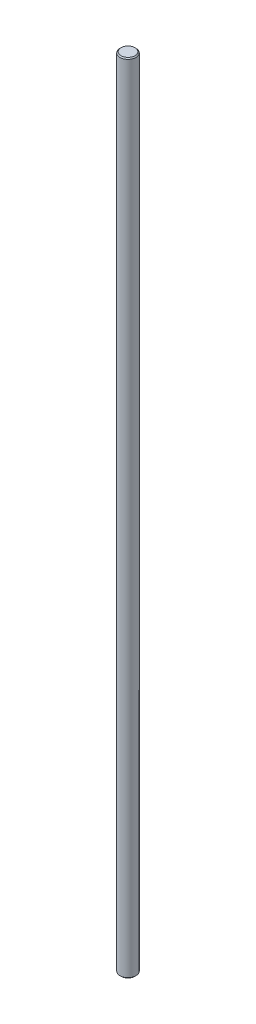
SolidWorks part; units mm, degrees
ref_plane "Front Plane" through (0, 0, 0) normal (0, 0, 1) x (1, 0, 0)
ref_plane "Top Plane" through (0, 0, 0) normal (0, 1, 0) x (1, 0, 0)
ref_plane "Right Plane" through (0, 0, 0) normal (1, 0, 0) x (0, 0, -1)
sketch "Sketch1" plane through (0, 0, 0) normal (0, 1, 0) x (1, 0, 0)
  circle A0 centre (0, 0) radius 4
  dimension "D1" = 8
extrude "Boss-Extrude1" add sketch "Sketch1" along normal blind 400
chamfer "Chamfer1" distance 0.508 angle 45 2 edges at (0, 0, 4) (0, 400, 4)
